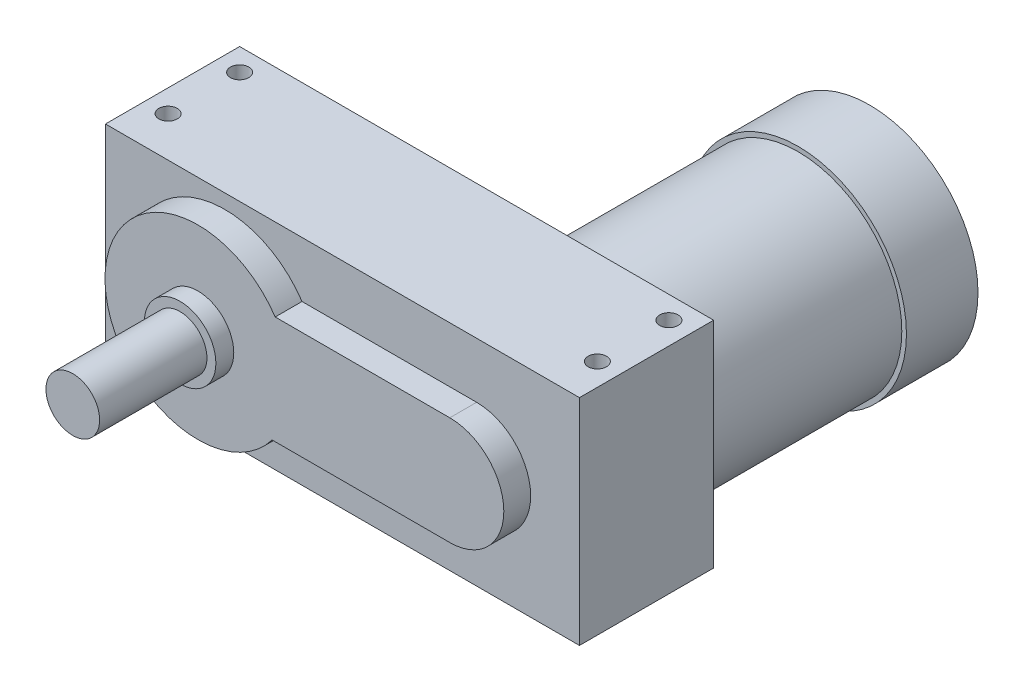
SolidWorks part; units mm, degrees
ref_plane "Front" through (0, 0, 0) normal (0, 0, 1) x (1, 0, 0)
ref_plane "Top" through (0, 0, 0) normal (0, 1, 0) x (1, 0, 0)
ref_plane "Right" through (0, 0, 0) normal (1, 0, 0) x (0, 0, -1)
sketch "Sketch1" plane through (0, 0, 0) normal (0, 0, 1) x (1, 0, 0)
  line L1 (-42.3672, 38.1) -> (125.9078, 38.1)
  line L2 (-42.3672, 38.1) -> (-42.3672, -38.1)
  line L3 (-42.3672, -38.1) -> (125.9078, -38.1)
  line L4 (125.9078, 38.1) -> (125.9078, -38.1)
  point P4 (-42.3672, 0)
  dimension "D1" = 76.2
  dimension "D2" = 42.3672
  dimension "D3" = 168.275
extrude "Extrude1" add sketch "Sketch1" against normal blind 57.15
sketch "Sketch2" plane through (0, 0, 0) normal (0, 0, 1) x (1, 0, 0)
  circle A0 centre (0, 0) radius 12.7
  dimension "D1" = 25.4
extrude "Extrude2" add sketch "Sketch2" along normal blind 6.35
sketch "Sketch3" plane through (0, 0, 6.35) normal (0, 0, 1) x (1, 0, 0)
  circle A0 centre (0, 0) radius 9.525
  dimension "D1" = 19.05
extrude "Extrude3" add sketch "Sketch3" along normal blind 38.1
hole_wizard "5/16-18 Tapped Hole1" positions "Sketch6" profile "Sketch5" tap size "5/16-18" standard "Ansi Inch"
sketch "Sketch6" plane through (0, -38.1, 0) normal (0, -1, 0) x (1, 0, 0)
  line L0 (125.9078, -57.15) -> (125.9078, 0) construction
  line L1 (-42.3672, -57.15) -> (125.9078, -57.15) construction
  point P0 (-34.4297, -23.8125)
  point P1 (-34.4297, -49.2125)
  point P2 (117.9703, -49.2125)
  point P3 (117.9703, -23.8125)
  dimension "D1" = 152.4
  dimension "D2" = 7.9375
  dimension "D3" = 25.4
  dimension "D4" = 7.9375
sketch "Sketch5" plane through (-34.4297, -38.1, -23.8125) normal (1, 0, 0) x (0, 0, -1)
  line L0 (0, 0) -> (0, 24.8846)
  line L1 (0, 24.8846) -> (3.2639, 22.9235)
  line L2 (3.2639, 22.9235) -> (3.2639, 0)
  line L5 (3.2639, 0) -> (0, 0)
  line L10 (0, 24.8846) -> (-3.2639, 22.9235) construction
  line L11 (0, -6.35) -> (0, 107.95) construction
  dimension "Tap Drill Dia." = 6.5278
  dimension "Tap Drill Depth" = 22.9235
  dimension "Drill Angle" = 118
cosmetic thread "Cosmetic Thread1" parameters "D1"=15.875, "D2"=7.9375
cosmetic thread "Cosmetic Thread2" parameters "D1"=15.875, "D2"=7.9375
cosmetic thread "Cosmetic Thread3" parameters "D1"=15.875, "D2"=7.9375
cosmetic thread "Cosmetic Thread4" parameters "D1"=15.875, "D2"=7.9375
sketch "Sketch7" plane through (0, 0, -57.15) normal (0, 0, -1) x (-1, 0, 0)
  line L0 (-125.9078, 0) -> (-87.8078, 0) construction
  line L1 (-125.9078, -38.1) -> (-125.9078, 38.1) construction
  circle A0 centre (-87.8078, 0) radius 36.83
  dimension "D1" = 73.66
  dimension "D2" = 38.1
extrude "Extrude4" add sketch "Sketch7" along normal blind 68.072
sketch "Sketch8" plane through (0, 0, -125.222) normal (0, 0, -1) x (-1, 0, 0)
  circle A0 centre (-87.8078, 0) radius 38.481
  dimension "D1" = 76.962
extrude "Extrude5" add sketch "Sketch8" along normal blind 25.4
hole_wizard "5/16-18 Tapped Hole2" positions "Sketch10" profile "Sketch9" tap size "5/16-18" standard "Ansi Inch"
sketch "Sketch10" plane through (0, 38.1, 0) normal (0, 1, 0) x (-1, 0, 0)
  point P1 (34.4297, -23.8125)
  point P2 (34.4297, -49.2125)
  point P4 (-117.9703, -49.2125)
  point P6 (-117.9703, -23.8125)
sketch "Sketch9" plane through (-34.4297, 38.1, -23.8125) normal (1, 0, 0) x (0, 0, 1)
  line L0 (0, 0) -> (0, 24.8841)
  line L1 (0, 24.8841) -> (3.2639, 22.923)
  line L2 (3.2639, 22.923) -> (3.2639, 0)
  line L5 (3.2639, 0) -> (0, 0)
  line L10 (0, 24.8841) -> (-3.2639, 22.923) construction
  line L11 (0, -6.35) -> (0, 107.95) construction
  dimension "Tap Drill Dia." = 6.5278
  dimension "Tap Drill Depth" = 22.923
  dimension "Drill Angle" = 118
cosmetic thread "Cosmetic Thread5" parameters "D1"=15.875, "D2"=7.9375
cosmetic thread "Cosmetic Thread6" parameters "D1"=15.875, "D2"=7.9375
cosmetic thread "Cosmetic Thread7" parameters "D1"=15.875, "D2"=7.9375
cosmetic thread "Cosmetic Thread8" parameters "D1"=15.875, "D2"=7.9375
cosmetic thread "Cosmetic Thread9" parameters "D1"=15.875, "D2"=7.9375
sketch "Sketch11" plane through (0, 0, 0) normal (0, 0, 1) x (1, 0, 0)
  line L0 (89.3931, 18.4102) -> (27.4114, 18.4102)
  line L1 (26.3186, -19.9412) -> (89.3931, -19.9412)
  arc A0 (27.4114, 18.4102) -> (26.3186, -19.9412) centre (0, 0) ccw
  arc A1 (89.3931, 18.4102) -> (89.3931, -19.9412) centre (89.3931, -0.7655) cw
  dimension "D1" = 33.02
extrude "Cut-Extrude1" cut sketch "Sketch11" against normal blind 9.525 flip side to cut
